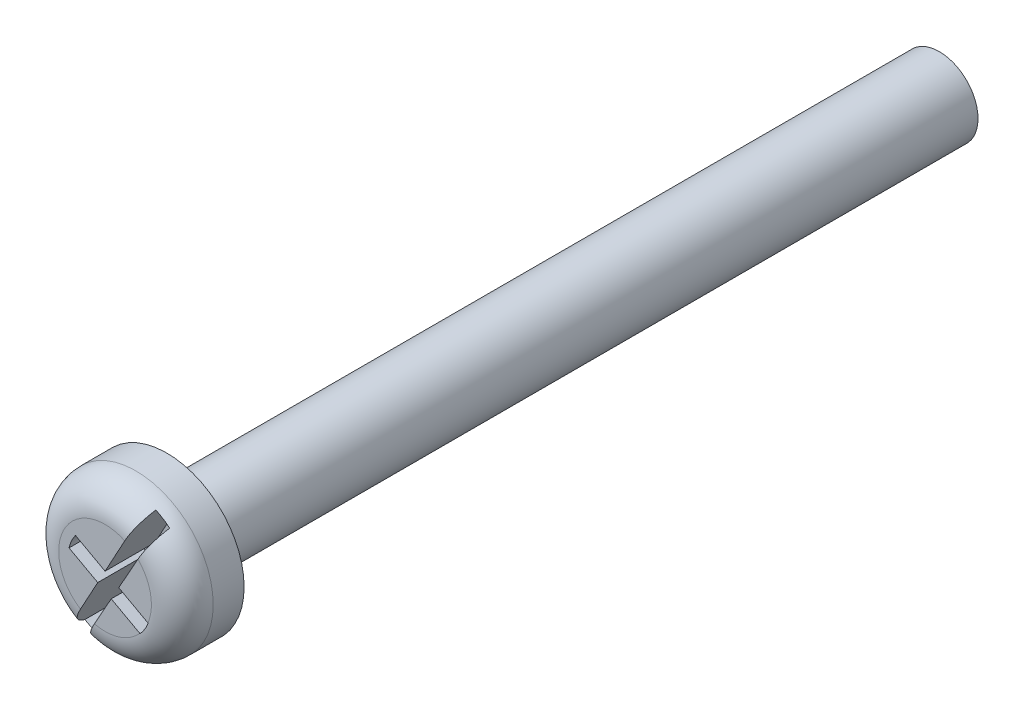
SolidWorks part; units mm, degrees
material "Stop odlewniczy stali"
ref_plane "Płaszczyzna przednia" through (0, 0, 0) normal (0, 0, 1) x (1, 0, 0)
ref_plane "Płaszczyzna górna" through (0, 0, 0) normal (0, 1, 0) x (1, 0, 0)
ref_plane "Płaszczyzna prawa" through (0, 0, 0) normal (1, 0, 0) x (0, 0, -1)
sketch "Szkic1" plane through (0, 0, 0) normal (0, 0, 1) x (1, 0, 0)
  circle A0 centre (-1.8605, 2.7321) radius 3
  dimension "D1" = 6
extrude "Dodanie-wyciągnięcie2" add sketch "Szkic1" along normal blind 2.4
sketch "Szkic2" plane through (0, 0, 0) normal (0, 0, -1) x (-1, 0, 0)
  circle A0 centre (1.8605, 2.7321) radius 1.5
extrude "Dodanie-wyciągnięcie3" add sketch "Szkic2" along normal blind 30
fillet "Zaokrąglenie2" radius 1.2 1 edges at (1.1395, 2.7321, 2.4)
sketch "Szkic3" plane through (0, 0, 2.4) normal (0, 0, 1) x (1, 0, 0)
  line L0 (-1.8595, 2.9591) -> (-0.5756, 5.3165)
  line L1 (-1.8595, 2.9591) -> (-3.0095, 3.5874)
  line L2 (-3.3345, 0.2508) -> (-2.1451, 2.4347)
  line L3 (-2.8199, 0.0102) -> (-1.6213, 2.1486)
  line L4 (-0.184, 2.0436) -> (-1.3294, 2.6694)
  line L5 (-0.4992, 1.5357) -> (-1.6213, 2.1486)
  line L6 (-1.3294, 2.6694) -> (-0.0393, 4.9711)
  line L7 (-2.1451, 2.4347) -> (-3.2587, 3.0429)
  arc A2 (-3.0095, 3.5874) -> (-3.2587, 3.0429) centre (-1.8605, 2.7321) ccw
  arc A3 (-0.0393, 4.9711) -> (-0.5756, 5.3165) centre (-1.8605, 2.7321) ccw
  arc A4 (-3.3345, 0.2508) -> (-2.8199, 0.0102) centre (-1.8605, 2.7321) ccw
  arc A6 (-0.4992, 1.5357) -> (-0.184, 2.0436) centre (-1.8605, 2.7321) ccw
extrude "Wytnij-wyciągnięcie1" cut sketch "Szkic3" against normal blind 1.94
